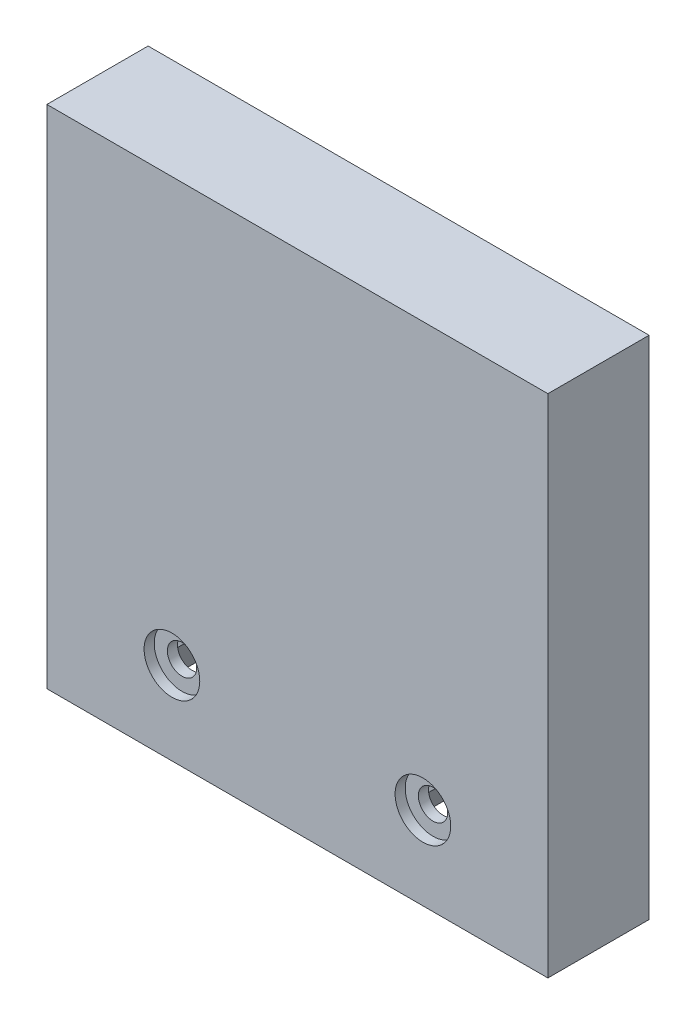
SolidWorks part; units mm, degrees
ref_plane "Front Plane" through (0, 0, 0) normal (0, 0, 1) x (1, 0, 0)
ref_plane "Top Plane" through (0, 0, 0) normal (0, 1, 0) x (1, 0, 0)
ref_plane "Right Plane" through (0, 0, 0) normal (1, 0, 0) x (0, 0, -1)
sketch "Sketch1" plane through (0, 0, 0) normal (0, 0, 1) x (1, 0, 0)
  line L2 (-22.8747, 0) -> (26.6253, 0)
  line L3 (-22.8747, 0) -> (-22.8747, 50.0006)
  line L4 (-22.8747, 50.0006) -> (26.6253, 50.0006)
  line L5 (26.6253, 0) -> (26.6253, 50.0006)
  dimension "D1" = 49.5
extrude "Boss-Extrude1" add sketch "Sketch1" along normal blind 10
sketch "Sketch3" plane through (0, 0, 0) normal (0, 0, -1) x (-1, 0, 0)
  line L6 (17.8713, -0.2) -> (14.7607, 5.1834)
  line L7 (-21.6216, -0.2) -> (17.8713, -0.2)
  line L8 (-21.6216, -0.2) -> (-18.5159, 5.1834)
  line L9 (-10.0393, 5.1834) -> (-8.0108, 1.67)
  line L10 (-8.0108, 1.67) -> (4.2572, 1.67)
  line L11 (4.2572, 1.67) -> (6.2841, 5.1834)
  arc A2 (6.2841, 5.1834) -> (14.7607, 5.1834) centre (10.5224, 8.1962) cw
  arc A3 (-18.5159, 5.1834) -> (-10.0393, 5.1834) centre (-14.2776, 8.1962) cw
extrude "Cut-Extrude1" cut sketch "Sketch3" against normal blind 8
sketch "Sketch4" plane through (0, 0, 8) normal (0, 0, -1) x (-1, 0, 0)
  line L0 (-19.4776, 8.1962) -> (-9.0776, 8.1962) construction
  line L1 (5.3224, 8.1962) -> (15.7224, 8.1962) construction
  arc A0 (-10.0393, 5.1834) -> (-18.5159, 5.1834) centre (-14.2776, 8.1962) ccw construction
  arc A1 (-10.0393, 5.1834) -> (-18.5159, 5.1834) centre (-14.2776, 8.1962) ccw construction
  circle A2 centre (-14.2776, 8.1962) radius 1.45
  arc A3 (14.7607, 5.1834) -> (6.2841, 5.1834) centre (10.5224, 8.1962) ccw construction
  arc A4 (14.7607, 5.1834) -> (6.2841, 5.1834) centre (10.5224, 8.1962) ccw construction
  circle A5 centre (10.5224, 8.1962) radius 1.45
extrude "Cut-Extrude2" cut sketch "Sketch4" against normal blind 8
sketch "Sketch5" plane through (0, 0, 10) normal (0, 0, 1) x (1, 0, 0)
  circle A0 centre (-10.5224, 8.1962) radius 2.75
  circle A1 centre (14.2776, 8.1962) radius 2.75
extrude "Cut-Extrude3" cut sketch "Sketch5" against normal blind 1
sketch "Sketch6" plane through (0, 0, 0) normal (0, 0, -1) x (-1, 0, 0)
  line L0 (-1.8753, 50.0006) -> (-1.8752, 0) construction
  line L1 (-26.6253, 50.0006) -> (22.8747, 50.0006) construction
  line L2 (17.7557, 0) -> (-21.5062, 0) construction
  circle A0 centre (-1.8753, 33.5006) radius 5
  dimension "D1" = 16.5
extrude "Cut-Extrude4" cut sketch "Sketch6" against normal blind 3
